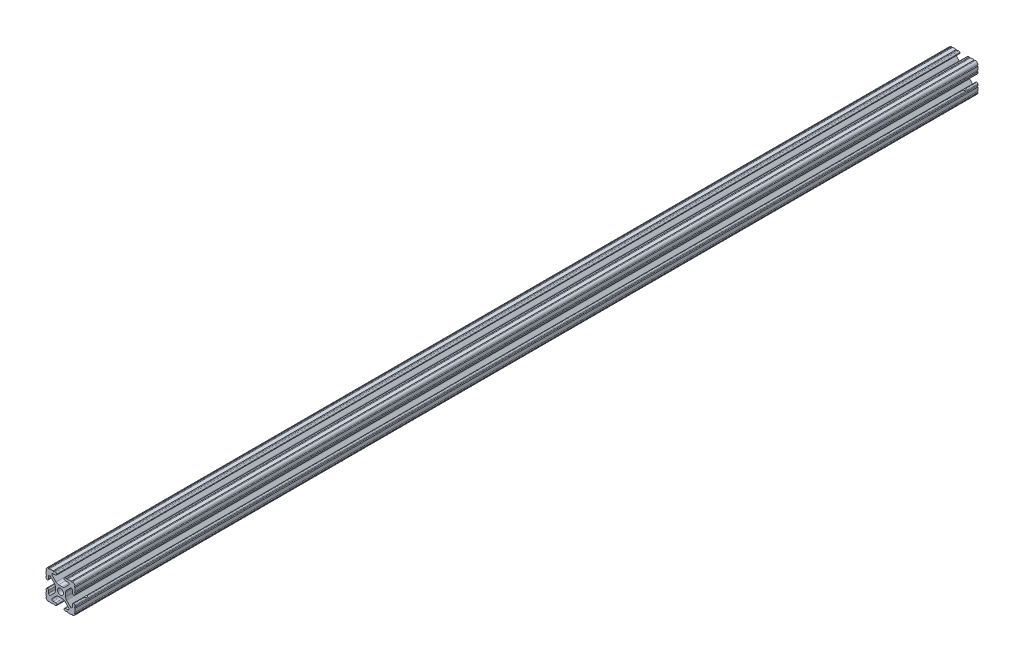
SolidWorks part; units mm, degrees
ref_plane "Front Plane" through (0, 0, 0) normal (0, 0, 1) x (1, 0, 0)
ref_plane "Top Plane" through (0, 0, 0) normal (0, 1, 0) x (1, 0, 0)
ref_plane "Right Plane" through (0, 0, 0) normal (1, 0, 0) x (0, 0, -1)
sketch "Sketch1" plane through (0, 0, 0) normal (0, 0, 1) x (1, 0, 0)
  line L88 (-7.1797, -8.6452) -> (-3.9523, -5.4237)
  line L89 (-1.7093, -4.4958) -> (1.7093, -4.4958)
  line L90 (3.9523, -5.4237) -> (7.1797, -8.6452)
  line L91 (6.4164, -10.4902) -> (4.2875, -10.4902)
  line L92 (3.2385, -11.5392) -> (3.2385, -11.651)
  line L93 (4.2875, -12.7) -> (5.3171, -12.7)
  line L94 (6.3331, -12.7) -> (9.5504, -12.7)
  line L95 (12.7, -9.5504) -> (12.7, -6.3331)
  line L96 (12.7, -5.3171) -> (12.7, -4.2875)
  line L97 (11.651, -3.2385) -> (11.5392, -3.2385)
  line L98 (10.4902, -4.2875) -> (10.4902, -6.4021)
  line L99 (8.7371, -7.1294) -> (5.441, -3.8408)
  line L100 (4.5085, -1.5932) -> (4.5085, 1.5932)
  line L101 (5.441, 3.8408) -> (8.7371, 7.1294)
  line L102 (10.4902, 6.4021) -> (10.4902, 4.2875)
  line L103 (11.5392, 3.2385) -> (11.651, 3.2385)
  line L104 (12.7, 4.2875) -> (12.7, 5.3171)
  line L105 (12.7, 6.3331) -> (12.7, 9.5504)
  line L106 (9.5504, 12.7) -> (6.3331, 12.7)
  line L107 (5.3171, 12.7) -> (4.2875, 12.7)
  line L108 (3.2385, 11.651) -> (3.2385, 11.5392)
  line L109 (4.2875, 10.4902) -> (6.4768, 10.4902)
  line L110 (7.207, 8.7244) -> (3.8983, 5.4232)
  line L111 (1.6558, 4.4958) -> (-1.6558, 4.4958)
  line L112 (-3.8983, 5.4232) -> (-7.207, 8.7244)
  line L113 (-6.4768, 10.4902) -> (-4.2875, 10.4902)
  line L114 (-3.2385, 11.5392) -> (-3.2385, 11.651)
  line L115 (-4.2875, 12.7) -> (-5.3171, 12.7)
  line L116 (-6.3331, 12.7) -> (-9.5504, 12.7)
  line L117 (-12.7, 9.5504) -> (-12.7, 6.3331)
  line L118 (-12.7, 5.3171) -> (-12.7, 4.2875)
  line L119 (-11.651, 3.2385) -> (-11.5392, 3.2385)
  line L120 (-10.4902, 4.2875) -> (-10.4902, 6.4021)
  line L121 (-8.7371, 7.1294) -> (-5.441, 3.8408)
  line L122 (-4.5085, 1.5932) -> (-4.5085, -1.5932)
  line L123 (-5.441, -3.8408) -> (-8.7371, -7.1294)
  line L124 (-10.4902, -6.4021) -> (-10.4902, -4.2875)
  line L125 (-11.5392, -3.2385) -> (-11.651, -3.2385)
  line L126 (-12.7, -4.2875) -> (-12.7, -5.3171)
  line L127 (-12.7, -6.3331) -> (-12.7, -9.5504)
  line L128 (-9.5504, -12.7) -> (-6.3331, -12.7)
  line L129 (-5.3171, -12.7) -> (-4.2875, -12.7)
  line L130 (-3.2385, -11.651) -> (-3.2385, -11.5392)
  line L131 (-4.2875, -10.4902) -> (-6.4164, -10.4902)
  circle A1 centre (0, 0) radius 2.6035
  arc A104 (-7.1797, -8.6452) -> (-6.4164, -10.4902) centre (-6.4164, -9.4098) ccw
  arc A105 (-1.7093, -4.4958) -> (-3.9523, -5.4237) centre (-1.7093, -7.6708) ccw
  arc A106 (3.9523, -5.4237) -> (1.7093, -4.4958) centre (1.7093, -7.6708) ccw
  arc A107 (6.4164, -10.4902) -> (7.1797, -8.6452) centre (6.4164, -9.4098) ccw
  arc A108 (4.2875, -10.4902) -> (3.2385, -11.5392) centre (4.2875, -11.5392) ccw
  arc A109 (3.2385, -11.651) -> (4.2875, -12.7) centre (4.2875, -11.651) ccw
  arc A110 (6.3331, -12.7) -> (5.3171, -12.7) centre (5.8251, -12.7) ccw
  arc A111 (10.5664, -12.6998) -> (9.5504, -12.7) centre (10.0584, -12.7) ccw
  arc A112 (10.5664, -12.6998) -> (12.6998, -10.5664) centre (10.5918, -10.5918) ccw
  arc A113 (12.7, -9.5504) -> (12.6998, -10.5664) centre (12.7, -10.0584) ccw
  arc A114 (12.7, -5.3171) -> (12.7, -6.3331) centre (12.7, -5.8251) ccw
  arc A115 (12.7, -4.2875) -> (11.651, -3.2385) centre (11.651, -4.2875) ccw
  arc A116 (11.5392, -3.2385) -> (10.4902, -4.2875) centre (11.5392, -4.2875) ccw
  arc A117 (8.7371, -7.1294) -> (10.4902, -6.4021) centre (9.4628, -6.4021) ccw
  arc A118 (4.5085, -1.5932) -> (5.441, -3.8408) centre (7.6835, -1.5932) ccw
  arc A119 (5.441, 3.8408) -> (4.5085, 1.5932) centre (7.6835, 1.5932) ccw
  arc A120 (10.4902, 6.4021) -> (8.7371, 7.1294) centre (9.4628, 6.4021) ccw
  arc A121 (10.4902, 4.2875) -> (11.5392, 3.2385) centre (11.5392, 4.2875) ccw
  arc A122 (11.651, 3.2385) -> (12.7, 4.2875) centre (11.651, 4.2875) ccw
  arc A123 (12.7, 6.3331) -> (12.7, 5.3171) centre (12.7, 5.8251) ccw
  arc A124 (12.6998, 10.5664) -> (12.7, 9.5504) centre (12.7, 10.0584) ccw
  arc A125 (12.6998, 10.5664) -> (10.5664, 12.6998) centre (10.5918, 10.5918) ccw
  arc A126 (9.5504, 12.7) -> (10.5664, 12.6998) centre (10.0584, 12.7) ccw
  arc A127 (5.3171, 12.7) -> (6.3331, 12.7) centre (5.8251, 12.7) ccw
  arc A128 (4.2875, 12.7) -> (3.2385, 11.651) centre (4.2875, 11.651) ccw
  arc A129 (3.2385, 11.5392) -> (4.2875, 10.4902) centre (4.2875, 11.5392) ccw
  arc A130 (7.207, 8.7244) -> (6.4768, 10.4902) centre (6.4768, 9.4563) ccw
  arc A131 (1.6558, 4.4958) -> (3.8983, 5.4232) centre (1.6558, 7.6708) ccw
  arc A132 (-3.8983, 5.4232) -> (-1.6558, 4.4958) centre (-1.6558, 7.6708) ccw
  arc A133 (-6.4768, 10.4902) -> (-7.207, 8.7244) centre (-6.4768, 9.4563) ccw
  arc A134 (-4.2875, 10.4902) -> (-3.2385, 11.5392) centre (-4.2875, 11.5392) ccw
  arc A135 (-3.2385, 11.651) -> (-4.2875, 12.7) centre (-4.2875, 11.651) ccw
  arc A136 (-6.3331, 12.7) -> (-5.3171, 12.7) centre (-5.8251, 12.7) ccw
  arc A137 (-10.5664, 12.6998) -> (-9.5504, 12.7) centre (-10.0584, 12.7) ccw
  arc A138 (-10.5664, 12.6998) -> (-12.6998, 10.5664) centre (-10.5918, 10.5918) ccw
  arc A139 (-12.7, 9.5504) -> (-12.6998, 10.5664) centre (-12.7, 10.0584) ccw
  arc A140 (-12.7, 5.3171) -> (-12.7, 6.3331) centre (-12.7, 5.8251) ccw
  arc A141 (-12.7, 4.2875) -> (-11.651, 3.2385) centre (-11.651, 4.2875) ccw
  arc A142 (-11.5392, 3.2385) -> (-10.4902, 4.2875) centre (-11.5392, 4.2875) ccw
  arc A143 (-8.7371, 7.1294) -> (-10.4902, 6.4021) centre (-9.4628, 6.4021) ccw
  arc A144 (-4.5085, 1.5932) -> (-5.441, 3.8408) centre (-7.6835, 1.5932) ccw
  arc A145 (-5.441, -3.8408) -> (-4.5085, -1.5932) centre (-7.6835, -1.5932) ccw
  arc A146 (-10.4902, -6.4021) -> (-8.7371, -7.1294) centre (-9.4628, -6.4021) ccw
  arc A147 (-10.4902, -4.2875) -> (-11.5392, -3.2385) centre (-11.5392, -4.2875) ccw
  arc A148 (-11.651, -3.2385) -> (-12.7, -4.2875) centre (-11.651, -4.2875) ccw
  arc A149 (-12.7, -6.3331) -> (-12.7, -5.3171) centre (-12.7, -5.8251) ccw
  arc A150 (-12.6998, -10.5664) -> (-12.7, -9.5504) centre (-12.7, -10.0584) ccw
  arc A151 (-12.6998, -10.5664) -> (-10.5664, -12.6998) centre (-10.5918, -10.5918) ccw
  arc A152 (-9.5504, -12.7) -> (-10.5664, -12.6998) centre (-10.0584, -12.7) ccw
  arc A153 (-5.3171, -12.7) -> (-6.3331, -12.7) centre (-5.8251, -12.7) ccw
  arc A154 (-4.2875, -12.7) -> (-3.2385, -11.651) centre (-4.2875, -11.651) ccw
  arc A155 (-3.2385, -11.5392) -> (-4.2875, -10.4902) centre (-4.2875, -11.5392) ccw
extrude "Boss-Extrude1" add sketch "Sketch1" along normal mid plane 793.47
sketch "Sketch2" plane through (4.5085, 0, 0) normal (1, 0, 0) x (0, 0, -1)
  line L0 (-396.735, -1.5932) -> (-396.735, 1.5932) construction
  line L1 (0, -1.5932) -> (0, 73.5485) construction
  line L2 (-396.735, -1.5932) -> (396.735, -1.5932) construction
  circle A0 centre (-386.035, 0) radius 3.5
  circle A1 centre (386.035, 0) radius 3.5
  dimension "D1" = 10.7
  dimension "D2" = 7
extrude "Cut-Extrude1" cut sketch "Sketch2" against normal through all both and the other way through all
